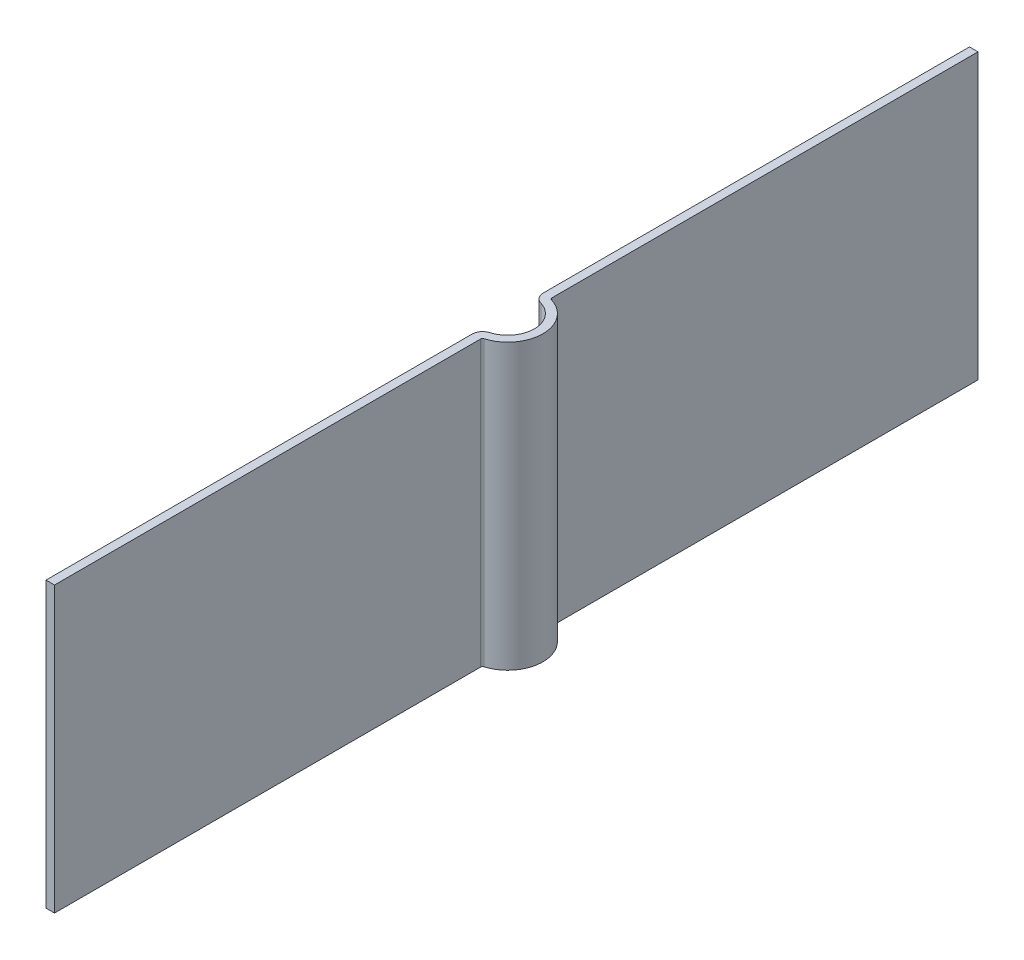
SolidWorks part; units mm, degrees
material "Chrome Stainless Steel"
ref_plane "Front Plane" through (0, 0, 0) normal (0, 0, 1) x (1, 0, 0)
ref_plane "Top Plane" through (0, 0, 0) normal (0, 1, 0) x (1, 0, 0)
ref_plane "Right Plane" through (0, 0, 0) normal (1, 0, 0) x (0, 0, -1)
sketch "Sketch2" plane through (0, 0, 0) normal (0, 1, 0) x (1, 0, 0)
  line L0 (0, 0.5031) -> (0, 6.5)
  line L1 (0, -55) -> (0, 55) construction
  line L2 (0, -0.5031) -> (0, -6.5)
  line L3 (-55, 0) -> (55, 0) construction
  arc A0 (0.1071, -0.3594) -> (0.1071, 0.3594) centre (0, 0) ccw
  arc A1 (0, 0.5031) -> (0.1071, 0.3594) centre (0.15, 0.5031) ccw
  arc A2 (0, -0.5031) -> (0.1071, -0.3594) centre (0.15, -0.5031) cw
  point P12 (0, 0.375)
  point P15 (0, -0.375)
  dimension "D1" = 0.75
  dimension "D4" = 0.15
  dimension "D2" = 6.5
  dimension "D3" = 6.5
extrude "Extrude-Thin1" add sketch "Sketch2" along normal blind 4 thin
